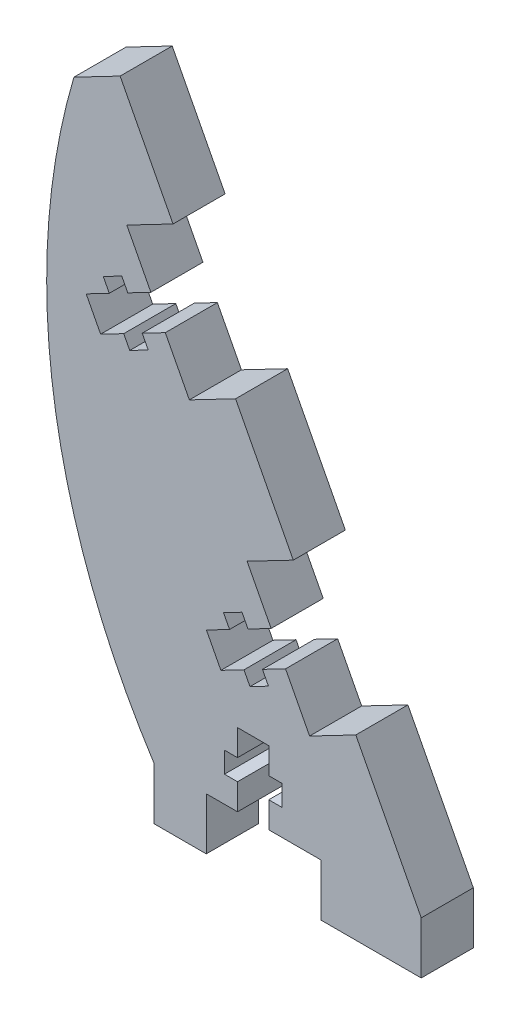
SolidWorks part; units mm, degrees
ref_plane "Front Plane" through (0, 0, 0) normal (0, 0, 1) x (1, 0, 0)
ref_plane "Top Plane" through (0, 0, 0) normal (0, 1, 0) x (1, 0, 0)
ref_plane "Right Plane" through (0, 0, 0) normal (1, 0, 0) x (0, 0, -1)
sketch "Sketch1" plane through (0, 0, 0) normal (0, 0, 1) x (1, 0, 0)
  line L0 (-20, 0) -> (0, 0)
  line L2 (0, 0) -> (-27.7049, 53.2206)
  arc A0 (-27.7049, 53.2206) -> (-20, 0) centre (34.29, 35.0278) ccw
  dimension "D1" = 62.5
  dimension "D2" = 20
  dimension "D3" = 60
extrude "Boss-Extrude1" add sketch "Sketch1" along normal blind 5
sketch "Sketch2" plane through (0, 0, 5) normal (0, 0, 1) x (1, 0, 0)
  line L0 (-20, 0) -> (0, 0) construction
  line L1 (-12, 7) -> (-9, 7)
  line L2 (-12, 7) -> (-12, 0)
  line L3 (-12, 0) -> (-9, 0)
  line L4 (-9, 7) -> (-9, 0)
  line L5 (-12, 7) -> (-9, 0) construction
  line L6 (-12, 0) -> (-9, 7) construction
  line L7 (-25.1408, 33.1352) -> (-18.9317, 36.3674)
  line L8 (-13.25, 4.5) -> (-7.75, 4.5)
  line L9 (-13.25, 4.5) -> (-13.25, 2.5)
  line L10 (-13.25, 2.5) -> (-7.75, 2.5)
  line L11 (-7.75, 4.5) -> (-7.75, 2.5)
  line L12 (-13.25, 4.5) -> (-7.75, 2.5) construction
  line L13 (-13.25, 2.5) -> (-7.75, 4.5) construction
  line L14 (-25.1408, 33.1352) -> (-26.526, 35.7962)
  line L15 (-18.9317, 36.3674) -> (-20.3169, 39.0285)
  line L16 (-26.526, 35.7962) -> (-20.3169, 39.0285)
  line L17 (-25.1408, 33.1352) -> (-20.3169, 39.0285) construction
  line L18 (-18.9317, 36.3674) -> (-26.526, 35.7962) construction
  line L19 (0, 0) -> (-27.7049, 53.2206) construction
  line L20 (-24.8857, 38.0594) -> (-22.3461, 33.1808)
  line L21 (-24.8857, 38.0594) -> (-23.1117, 38.9829)
  line L22 (-22.3461, 33.1808) -> (-20.572, 34.1043)
  line L23 (-23.1117, 38.9829) -> (-20.572, 34.1043)
  line L24 (-24.8857, 38.0594) -> (-20.572, 34.1043) construction
  line L25 (-22.3461, 33.1808) -> (-23.1117, 38.9829) construction
  line L26 (-13.5971, 10.9599) -> (-7.388, 14.1922)
  line L27 (-13.5971, 10.9599) -> (-14.9823, 13.621)
  line L28 (-7.388, 14.1922) -> (-8.7732, 16.8532)
  line L29 (-14.9823, 13.621) -> (-8.7732, 16.8532)
  line L30 (-13.5971, 10.9599) -> (-8.7732, 16.8532) construction
  line L31 (-7.388, 14.1922) -> (-14.9823, 13.621) construction
  line L32 (-13.342, 15.8841) -> (-10.8023, 11.0055)
  line L33 (-13.342, 15.8841) -> (-11.5679, 16.8076)
  line L34 (-10.8023, 11.0055) -> (-9.0283, 11.929)
  line L35 (-11.5679, 16.8076) -> (-9.0283, 11.929)
  line L36 (-13.342, 15.8841) -> (-9.0283, 11.929) construction
  line L37 (-10.8023, 11.0055) -> (-11.5679, 16.8076) construction
  line L38 (-22.7289, 36.0818) -> (-11.1851, 13.9066) construction
  line L39 (-16.957, 24.9942) -> (-13.8525, 26.6103) construction
  point P0 (-10.5, 3.5)
  point P7 (-10.5, 3.5)
  point P13 (-22.7289, 36.0818)
  point P20 (-22.7289, 36.0818)
  point P21 (-11.1851, 13.9066)
  point P22 (-11.1851, 13.9066)
  arc M1 (-27.7049, 53.2206) -> (-20, 0) centre (34.29, 35.0278) ccw
  line M2 (-20, 0) -> (0, 0)
  line M3 (0, 0) -> (-27.7049, 53.2206)
  dimension "D1" = 5.5
  dimension "D2" = 3
  dimension "D3" = 2
  dimension "D4" = 7
  dimension "D5" = 25
  dimension "D6" = 8
extrude "Cut-Extrude1" cut sketch "Sketch2" against normal blind 5 flip side to cut contours L33 L35 L29 L7 L23 L22 L20 L14 L16 L21 L2 L10 L9 L8 L1 L4 L11 L26 L34 L32 L27 M3 M1 M2
sketch "Sketch3" plane through (0, 0, 5) normal (0, 0, 1) x (1, 0, 0)
  line L0 (-27.7049, 53.2206) -> (-22.6257, 43.4635)
  line L1 (-27.7049, 53.2206) -> (-23.2699, 55.5294)
  line L2 (-22.6257, 43.4635) -> (-18.1906, 45.7723)
  line L3 (-23.2699, 55.5294) -> (-18.1906, 45.7723)
  line L4 (-20.3169, 39.0285) -> (-27.7049, 53.2206) construction
  line L5 (-16.623, 31.9324) -> (-11.082, 21.2883)
  line L6 (-16.623, 31.9324) -> (-12.1879, 34.2411)
  line L7 (-11.082, 21.2883) -> (-6.6469, 23.597)
  line L8 (-12.1879, 34.2411) -> (-6.6469, 23.597)
  line L9 (-8.7732, 16.8532) -> (-18.9317, 36.3674) construction
  line L10 (0, 0) -> (-5.0792, 9.7571)
  line L12 (-5.0792, 9.7571) -> (-0.6442, 12.0659)
  line L13 (5.6369, 0) -> (-0.6442, 12.0659)
  line L14 (0, 0) -> (-7.388, 14.1922) construction
  line L15 (-20, 0) -> (-12, 0) construction
  line L16 (-20, 0) -> (-15, 0)
  line L17 (-20, 0) -> (-20, -5)
  line L18 (-20, -5) -> (-15, -5)
  line L19 (-15, 0) -> (-15, -5)
  line L20 (-12, 2.5) -> (-12, 0) construction
  line L21 (0, 0) -> (-4, 0)
  line L23 (-2.7964, -5) -> (-4, -5)
  line L24 (-4, 0) -> (-4, -5)
  line L25 (-9, 2.5) -> (-9, 0) construction
  line L27 (-2.7964, -5) -> (5.6369, -5)
  line L30 (5.6369, -5) -> (5.6369, 0)
  point P35 (-9, 1.25)
  dimension "D1" = 5
  dimension "D2" = 5
  dimension "D3" = 5
  dimension "D4" = 5
  dimension "D5" = 5
  dimension "D6" = 3
  dimension "D7" = 5
extrude "Boss-Extrude2" add sketch "Sketch3" against normal blind 5
